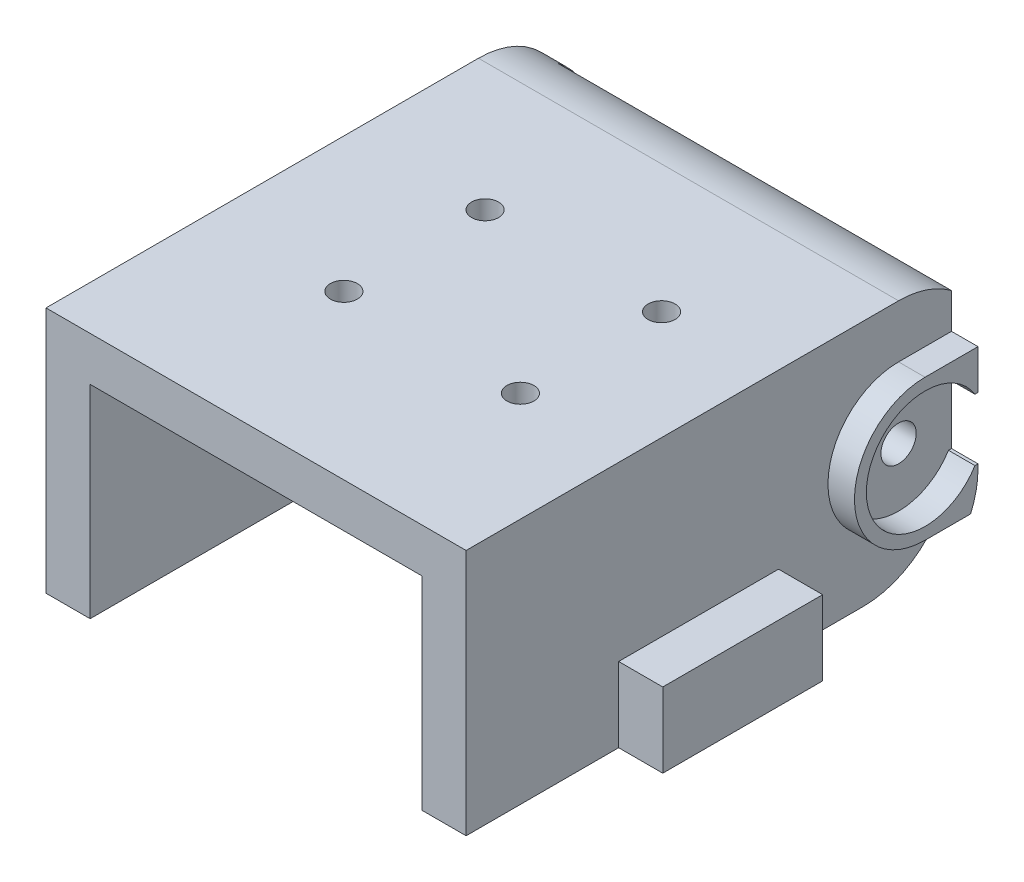
SolidWorks part; units mm, degrees
ref_plane "Front Plane" through (0, 0, 0) normal (0, 0, 1) x (1, 0, 0)
ref_plane "Top Plane" through (0, 0, 0) normal (0, 1, 0) x (1, 0, 0)
ref_plane "Right Plane" through (0, 0, 0) normal (1, 0, 0) x (0, 0, -1)
sketch "Sketch1" plane through (0, 0, 0) normal (0, 0, 1) x (1, 0, 0)
  line L1 (-23.8, 14) -> (23.8, 14)
  line L2 (-23.8, 14) -> (-23.8, -14)
  line L3 (-23.8, -14) -> (23.8, -14)
  line L4 (23.8, 14) -> (23.8, -14)
  line L5 (-23.8, 14) -> (23.8, -14) construction
  line L6 (-23.8, -14) -> (23.8, 14) construction
  point P0 (0, 0)
  dimension "D1" = 47.6
  dimension "D2" = 28
extrude "Boss-Extrude1" add sketch "Sketch1" along normal blind 55
sketch "Sketch3" plane through (23.8, 0, 0) normal (1, 0, 0) x (0, 0, -1)
  line L0 (0, -14) -> (0, 14) construction
  line L1 (-55, 14) -> (0, 14) construction
  circle A0 centre (-6, 0) radius 2
  dimension "D1" = 4
  dimension "D2" = 6
  dimension "D3" = 14
extrude "Cut-Extrude1" cut sketch "Sketch3" against normal blind 3
sketch "Sketch4" plane through (23.8, 0, 0) normal (1, 0, 0) x (0, 0, -1)
  line L0 (-55, -14) -> (0, -14) construction
  line L1 (-37.7174, -14) -> (-19.6014, -14)
  line L2 (-37.7174, -14) -> (-37.7174, -5.5367)
  line L3 (-37.7174, -5.5367) -> (-19.6014, -5.5367)
  line L4 (-19.6014, -14) -> (-19.6014, -5.5367)
extrude "Boss-Extrude2" add sketch "Sketch4" along normal blind 5
sketch "Sketch5" plane through (23.8, 0, 0) normal (1, 0, 0) x (0, 0, -1)
  line L1 (-6, 6.65) -> (2.4931, 6.65)
  line L2 (-6, 6.65) -> (-6, -6.5)
  line L3 (-6, -6.5) -> (2.4931, -6.5)
  line L4 (2.4931, 6.65) -> (2.4931, -6.5)
  line L5 (-6, 8) -> (2.4931, 8)
  line L6 (-6, 8) -> (-6, -8)
  line L7 (-6, -8) -> (2.4931, -8)
  line L8 (2.4931, 8) -> (2.4931, -8)
  line L9 (-6, 3.5) -> (2.4931, 3.5)
  line L10 (-6, 3.5) -> (-6, -3.5)
  line L11 (-6, -3.5) -> (2.4931, -3.5)
  line L12 (2.4931, 3.5) -> (2.4931, -3.5)
  circle A0 centre (-6, 0) radius 3.5
  circle A1 centre (-6, 0) radius 6.65
  circle A2 centre (-6, 0) radius 8
  line M6 (0, -14) -> (0, 14)
  dimension "D1" = 7
  dimension "D2" = 13.3
  dimension "D3" = 16
extrude "Boss-Extrude4" add sketch "Sketch5" along normal blind 3 contours L1 A2 L6 | A2 L1 L5 M6 | L6 A2 L3 | A2 L7 L3 M6 | A2 L1 M6 | A2 L3 M6 | A2 L1 A1 L9 M6 | L3 A2 L11 A1 M6 | L6 A2 A1
sketch "Sketch6" plane through (-23.8, 0, 0) normal (-1, 0, 0) x (0, 0, 1)
  line L0 (0, 0) -> (6, 0) construction
  line L1 (0, 14) -> (0, -14) construction
  line L3 (6, 3.5) -> (-6.6051, 3.5)
  line L4 (6, 3.5) -> (6, -3.5)
  line L5 (6, -3.5) -> (-6.6051, -3.5)
  line L6 (-6.6051, 3.5) -> (-6.6051, -3.5)
  circle A0 centre (6, 0) radius 8
  circle A1 centre (6, 0) radius 10
  circle A2 centre (6, 0) radius 3.5
  line M2 (0, 14) -> (0, -14)
  dimension "D2" = 7
  dimension "D1" = 6
extrude "Boss-Extrude5" add sketch "Sketch6" along normal blind 3 contours A1 A0 M2 | L5 A1 A0 M2 | A1 L3 A0 M2
sketch "Sketch8" plane through (0, 0, 0) normal (0, 0, -1) x (-1, 0, 0)
  line L0 (23.8, -14) -> (-23.8, -14) construction
  line L1 (23.8, 14) -> (20.8, 14)
  line L2 (23.8, 14) -> (23.8, -14)
  line L3 (23.8, -14) -> (20.8, -14)
  line L4 (20.8, 14) -> (20.8, -14)
  dimension "D1" = 3
extrude "Boss-Extrude7" add sketch "Sketch8" along normal blind 4
fillet "Fillet1" radius 10 2 edges at (-22.3, 14, -4) (1.5, -14, 0)
fillet "Fillet2" radius 10 1 edges at (-22.3, -14, -4)
ref_plane "Plane1" through (33.8, 0, 0) normal (1, 0, 0) x (0, 0, -1)
sketch "Sketch9" plane through (0, 14, 0) normal (0, 1, 0) x (1, 0, 0)
  line L1 (-23.8, -55) -> (-23.8, -6) construction
  line L2 (-20.8, 0) -> (23.8, 0) construction
  circle A0 centre (-8.55, -20.5) radius 1.5302
  circle A1 centre (11.45, -20.5) radius 1.5302
  circle A2 centre (11.45, -36.5) radius 1.5302
  circle A3 centre (-8.55, -36.5) radius 1.5302
  dimension "D1" = 20.5
  dimension "D2" = 15.25
  dimension "D5" = 20
  dimension "D6" = 16
  dimension "D7" = 20
  dimension "D3" = 2
  dimension "D4" = 2
extrude "Cut-Extrude2" cut sketch "Sketch9" against normal through all
sketch "Sketch10" plane through (0, 0, 55) normal (0, 0, 1) x (1, 0, 0)
  line L6 (-23.8, -14) -> (23.8, -14) construction
  line L7 (-18.8, -14) -> (18.8, -14)
  line L8 (-18.8, -14) -> (-18.8, 9)
  line L9 (-18.8, 9) -> (18.8, 9)
  line L10 (18.8, -14) -> (18.8, 9)
  line L11 (23.8, 14) -> (-23.8, 14) construction
  line L12 (-23.8, 14) -> (-23.8, -14) construction
  line L13 (23.8, -14) -> (23.8, 14) construction
  dimension "D1" = 5
  dimension "D2" = 5
  dimension "D3" = 5
extrude "Cut-Extrude4" cut sketch "Sketch10" against normal blind 40
